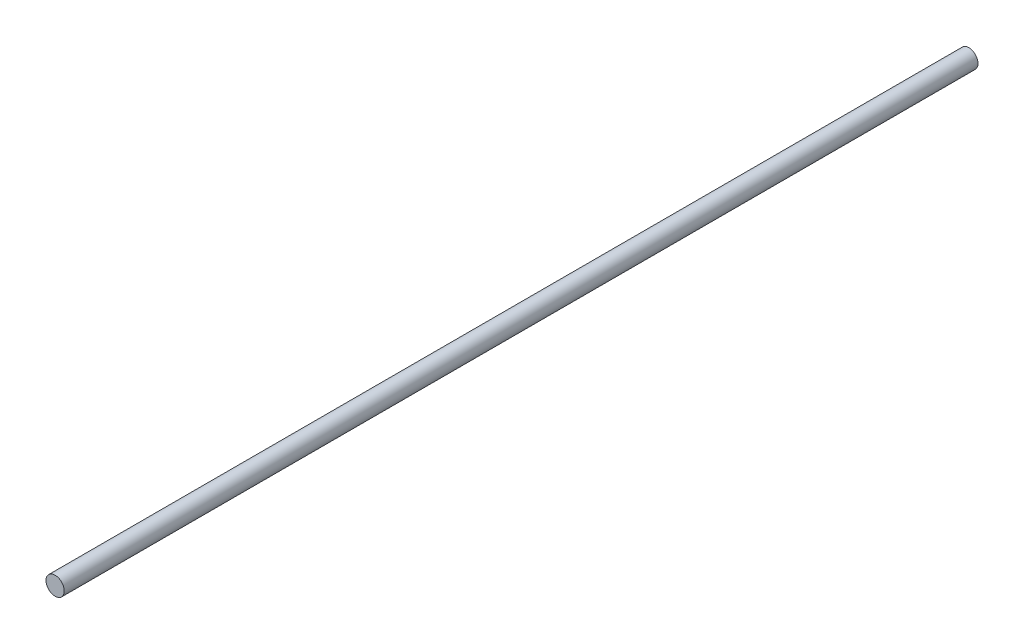
SolidWorks part; units mm, degrees
material "Plain Carbon Steel"
ref_plane "Front Plane" through (0, 0, 0) normal (0, 0, 1) x (1, 0, 0)
ref_plane "Top Plane" through (0, 0, 0) normal (0, 1, 0) x (1, 0, 0)
ref_plane "Right Plane" through (0, 0, 0) normal (1, 0, 0) x (0, 0, -1)
sketch "Sketch2" plane through (0, 0, 0) normal (0, 0, 1) x (1, 0, 0)
  circle A0 centre (0, 0) radius 3.048
  dimension "D1" = 6.096
extrude "Boss-Extrude1" add sketch "Sketch2" along normal blind 304.8
